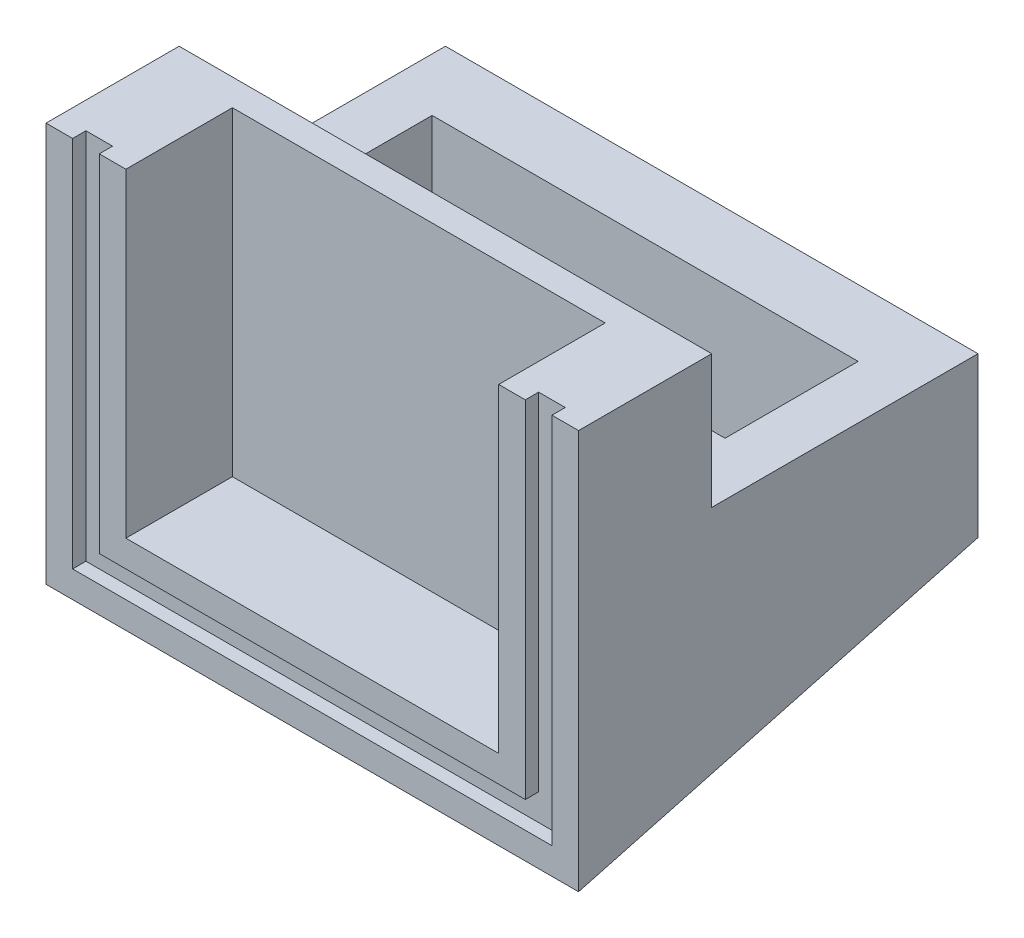
SolidWorks part; units mm, degrees
ref_plane "Front Plane" through (0, 0, 0) normal (0, 0, 1) x (1, 0, 0)
ref_plane "Top Plane" through (0, 0, 0) normal (0, 1, 0) x (1, 0, 0)
ref_plane "Right Plane" through (0, 0, 0) normal (1, 0, 0) x (0, 0, -1)
sketch "Sketch1" plane through (0, 0, 0) normal (0, 1, 0) x (1, 0, 0)
  line L1 (-10, -5) -> (10, -5)
  line L2 (-10, -5) -> (-10, 5)
  line L3 (-10, 5) -> (10, 5)
  line L4 (10, -5) -> (10, 5)
  line L5 (-10, -5) -> (10, 5) construction
  line L6 (-10, 5) -> (10, -5) construction
  point P0 (0, 0)
  dimension "D1" = 20
  dimension "D2" = 10
extrude "Boss-Extrude1" add sketch "Sketch1" along normal blind 10
sketch "Sketch2" plane through (0, 10, 0) normal (0, 1, 0) x (1, 0, 0)
  line L1 (-8, -2.5) -> (8, -2.5)
  line L2 (-8, -2.5) -> (-8, 2.5)
  line L3 (-8, 2.5) -> (8, 2.5)
  line L4 (8, -2.5) -> (8, 2.5)
  line L5 (-8, -2.5) -> (8, 2.5) construction
  line L6 (-8, 2.5) -> (8, -2.5) construction
  point P0 (0, 0)
  dimension "D1" = 16
  dimension "D2" = 5
extrude "Cut-Extrude1" cut sketch "Sketch2" against normal through all
sketch "Sketch3" plane through (0, 0, 5) normal (0, 0, 1) x (1, 0, 0)
  line L0 (-10, 0) -> (10, 0) construction
  line L1 (10, 15) -> (-10, 15)
  line L2 (10, 15) -> (10, 0)
  line L3 (10, 0) -> (-10, 0)
  line L4 (-10, 15) -> (-10, 0)
  line L5 (10, 15) -> (-10, 0) construction
  line L6 (10, 0) -> (-10, 15) construction
  line L7 (0, 0) -> (0, 10) construction
  line L8 (-10, 10) -> (10, 10) construction
  point P0 (0, 7.5)
  dimension "D1" = 0
  dimension "D2" = 20
  dimension "D3" = 0
  dimension "D4" = 15
extrude "Boss-Extrude2" add sketch "Sketch3" along normal blind 5
sketch "Sketch4" plane through (0, 0, 10) normal (0, 0, 1) x (1, 0, 0)
  line L1 (7, 3) -> (-7, 3)
  line L2 (-7, 3) -> (-7, 15)
  line L3 (-7, 15) -> (7, 15)
  line L4 (-10, 0) -> (10, 0) construction
  line L5 (-10, 15) -> (-10, 0) construction
  line L6 (7, 3) -> (7, 15)
  line L7 (0, 0) -> (0, 15) construction
  line L8 (10, 15) -> (-10, 15) construction
  point P13 (0, 3)
  dimension "D1" = 3
  dimension "D2" = 3
extrude "Cut-Extrude2" cut sketch "Sketch4" against normal blind 4
sketch "Sketch5" plane through (0, 0, 10) normal (0, 0, 1) x (1, 0, 0)
  line L0 (-8.5, 15) -> (-8.5, 1.5) construction
  line L1 (-8.5, 1.5) -> (0, 1.5) construction
  line L2 (0, 0) -> (0, 15) construction
  line L3 (-10, 0) -> (10, 0) construction
  line L4 (7, 15) -> (-7, 15) construction
  line L5 (-7, 15) -> (-7, 3) construction
  line L6 (8.5, 15) -> (8.5, 1.5) construction
  line L7 (8.5, 1.5) -> (0, 1.5) construction
  line L8 (-9, 15) -> (-9, 1)
  line L9 (-9, 1) -> (0, 1)
  line L10 (9, 1) -> (0, 1)
  line L12 (9, 15) -> (9, 1)
  line L13 (-8, 15) -> (-8, 2)
  line L14 (-8, 2) -> (0, 2)
  line L15 (8, 2) -> (0, 2)
  line L16 (8, 15) -> (8, 2)
  line L17 (-9, 15) -> (-8, 15)
  line L18 (9, 15) -> (8, 15)
  dimension "D1" = 1.5
  dimension "D2" = 1.5
  dimension "D3" = 0.5
  dimension "D4" = 0.5
extrude "Cut-Extrude3" cut sketch "Sketch5" against normal blind 0.5
sketch "Sketch7" plane through (10, 0, 0) normal (1, 0, 0) x (0, 0, -1)
  line L0 (-10, 0) -> (5, 4.0192)
  line L1 (5, 10) -> (5, 0) construction
  line L2 (-10, 0) -> (5, 0) construction
  line L3 (5, 4.0192) -> (5, 0)
  line L4 (5, 0) -> (-10, 0)
  line L5 (-10, 0) -> (-9.9886, -0.0068)
  line M2 (-10, 0) -> (5, 0)
  line M3 (5, 0) -> (5, 10)
  dimension "D1" = 15
extrude "Cut-Extrude4" cut sketch "Sketch7" against normal through all contours L0 M2 M3
